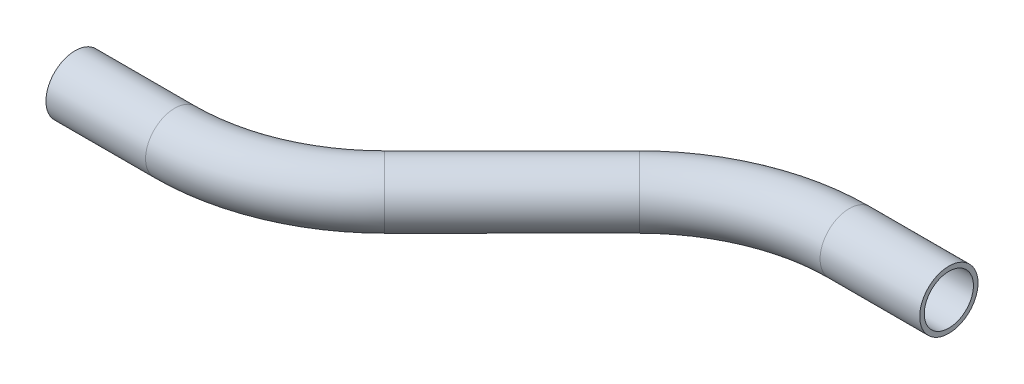
SolidWorks part; units mm, degrees
ref_plane "Front Plane" through (0, 0, 0) normal (0, 0, 1) x (1, 0, 0)
ref_plane "Top Plane" through (0, 0, 0) normal (0, 1, 0) x (1, 0, 0)
ref_plane "Right Plane" through (0, 0, 0) normal (1, 0, 0) x (0, 0, -1)
sketch "Sketch1" plane through (0, 0, 0) normal (0, 1, 0) x (1, 0, 0)
  line L0 (0, 0) -> (27.1277, 0)
  line L1 (67.5388, 16.7388) -> (102.2173, 51.4173)
  line L2 (142.6284, 68.1561) -> (169.7561, 68.1561)
  arc A0 (102.2173, 51.4173) -> (142.6284, 68.1561) centre (142.6284, 11.0061) cw
  arc A1 (27.1277, 0) -> (67.5388, 16.7388) centre (27.1277, 57.15) ccw
  point P7 (118.9561, 68.1561)
  point P10 (50.8, 0)
  dimension "D5" = 57.15
  dimension "D1" = 50.8
  dimension "D2" = 50.8
  dimension "D3" = 135
  dimension "D4" = 68.1561
ref_plane "Plane1" through (0, 0, 0) normal (1, 0, 0) x (0, 0, -1)
sketch "Sketch2" plane through (0, 0, 0) normal (1, 0, 0) x (0, 0, -1)
  circle A0 centre (0, 0) radius 7.9375
  circle A1 centre (0, 0) radius 6.6929
  dimension "D1" = 15.875
  dimension "D2" = 1.2446
sweep "Sweep1" add profiles "Sketch2" path "Sketch1"
